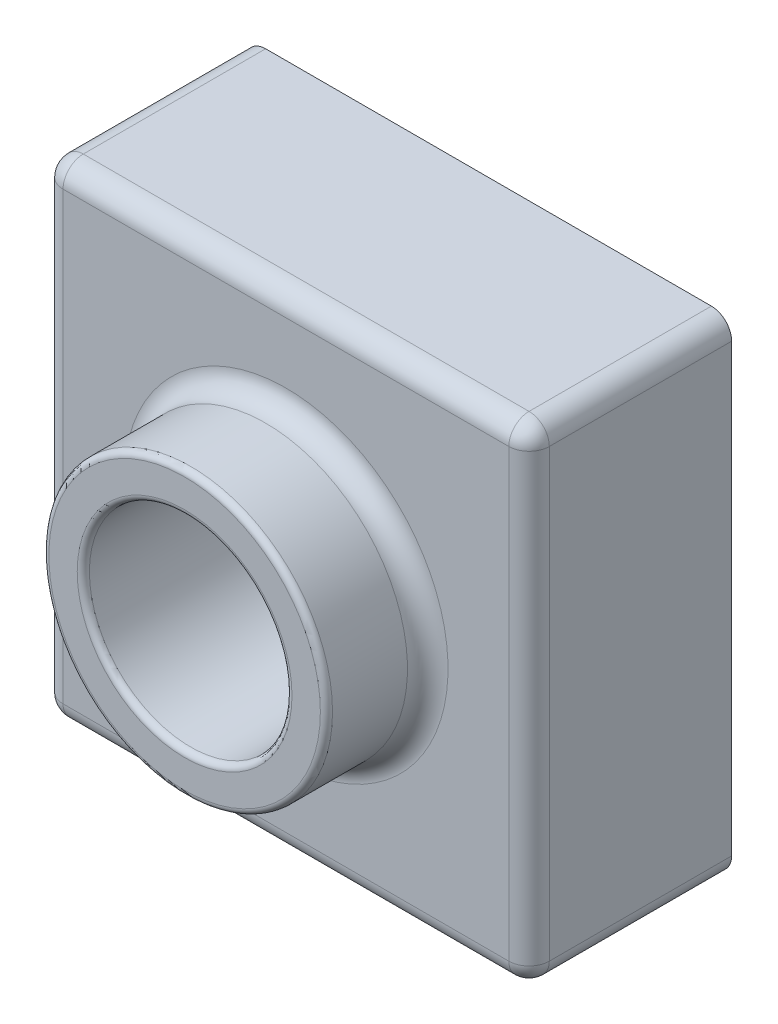
SolidWorks part; units mm, degrees
ref_plane "Front Plane" through (0, 0, 0) normal (0, 0, 1) x (1, 0, 0)
ref_plane "Top Plane" through (0, 0, 0) normal (0, 1, 0) x (1, 0, 0)
ref_plane "Right Plane" through (0, 0, 0) normal (1, 0, 0) x (0, 0, -1)
other "Configuration Table"
sketch "Sketch2" plane through (0, 0, 0) normal (0, 0, 1) x (1, 0, 0)
  line L1 (0, 0) -> (120, 0)
  line L2 (0, 0) -> (0, 120)
  line L3 (0, 120) -> (120, 120)
  line L4 (120, 0) -> (120, 120)
  dimension "D1" = 120
  dimension "D2" = 120
extrude "Boss-Extrude1" add sketch "Sketch2" along normal blind 50
sketch "Sketch4" plane through (0, 0, 50) normal (0, 0, 1) x (1, 0, 0)
  line L0 (120, 120) -> (0, 120) construction
  line L1 (0, 120) -> (0, 0) construction
  circle A0 centre (60, 60) radius 35
  dimension "D1" = 60
  dimension "D3" = 70
  dimension "D2" = 60
extrude "Boss-Extrude2" add sketch "Sketch4" along normal blind 25
sketch "Sketch6" plane through (0, 0, 75) normal (0, 0, 1) x (1, 0, 0)
  circle A0 centre (60, 60) radius 25
  dimension "D1" = 50
extrude "Cut-Extrude1" cut sketch "Sketch6" against normal through all
fillet "Fillet1" radius 5 9 edges at (25, 60, 50) (60, 120, 50) (120, 60, 50) (60, 0, 50) (0, 60, 50) (0, 0, 25) (120, 0, 25) (120, 120, 25) (0, 120, 25)
fillet "Fillet2" radius 1.5 2 edges at (95, 60, 75) (85, 60, 75)
shell "Shell1" thickness 2
